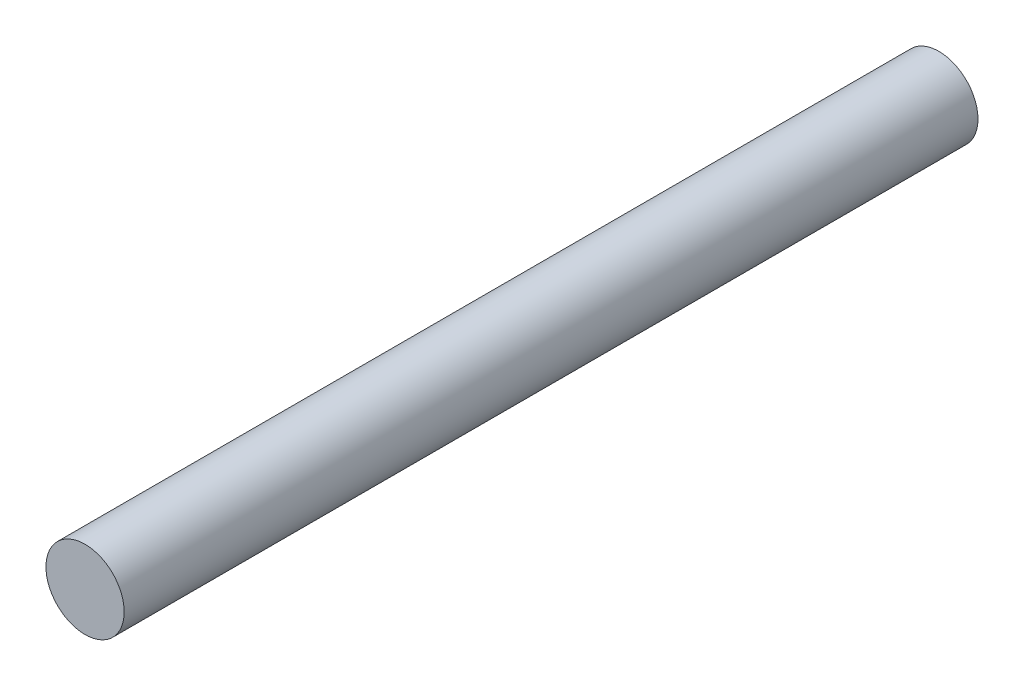
SolidWorks part; units mm, degrees
ref_plane "Přední rovina" through (0, 0, 0) normal (0, 0, 1) x (1, 0, 0)
ref_plane "Horní rovina" through (0, 0, 0) normal (0, 1, 0) x (1, 0, 0)
ref_plane "Pravá rovina" through (0, 0, 0) normal (1, 0, 0) x (0, 0, -1)
sketch "Skica1" plane through (0, 0, 0) normal (0, 0, 1) x (1, 0, 0)
  circle A0 centre (0, 0) radius 1.65
  dimension "D1" = 3.3
extrude "Přidat vysunutím1" add sketch "Skica1" along normal blind 36
